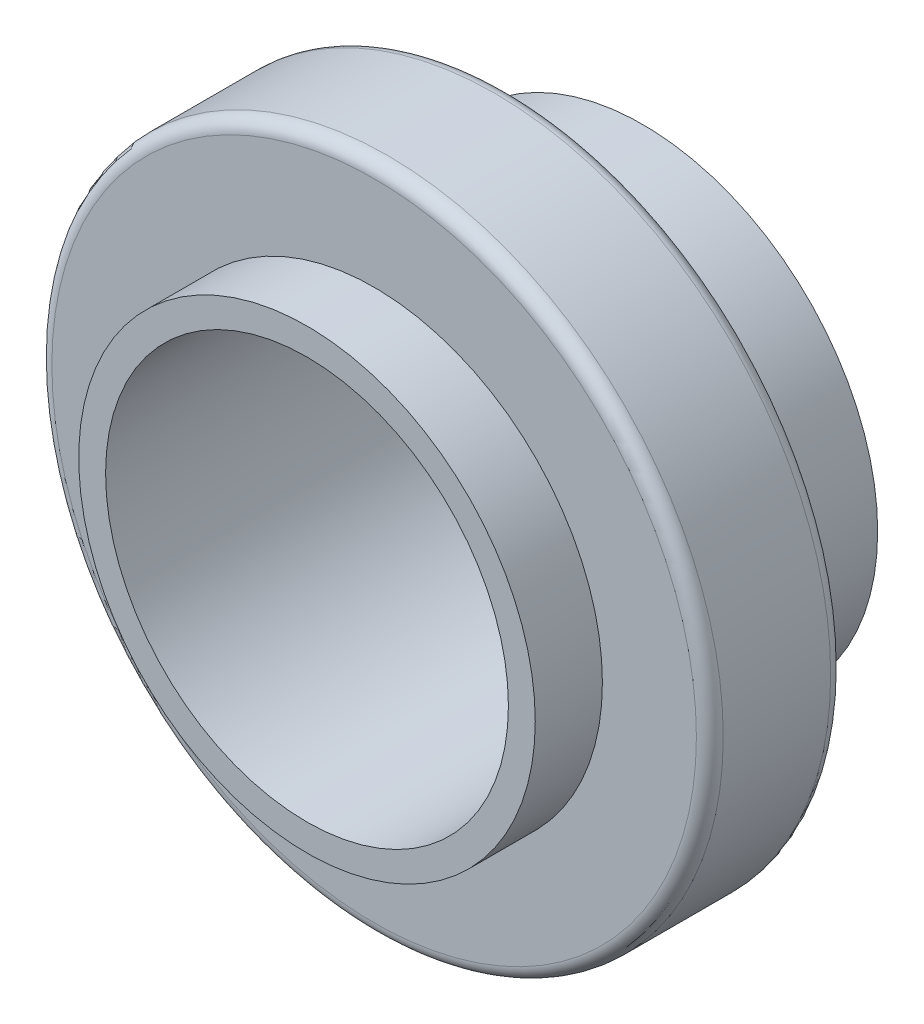
SolidWorks part; units mm, degrees
ref_plane "Front Plane" through (0, 0, 0) normal (0, 0, 1) x (1, 0, 0)
ref_plane "Top Plane" through (0, 0, 0) normal (0, 1, 0) x (1, 0, 0)
ref_plane "Right Plane" through (0, 0, 0) normal (1, 0, 0) x (0, 0, -1)
sketch "Sketch1" plane through (0, 0, 0) normal (0, 0, 1) x (1, 0, 0)
  circle A0 centre (0, 0) radius 17.5
  dimension "D1" = 35
extrude "Boss-Extrude1" add sketch "Sketch1" along normal blind 10
sketch "Sketch2" plane through (0, 0, 10) normal (0, 0, 1) x (1, 0, 0)
  circle A0 centre (0, 0) radius 25
  dimension "D1" = 50
extrude "Boss-Extrude2" add sketch "Sketch2" along normal blind 10
sketch "Sketch3" plane through (0, 0, 20) normal (0, 0, 1) x (1, 0, 0)
  circle A0 centre (0, 0) radius 17
  dimension "D1" = 34
extrude "Boss-Extrude3" add sketch "Sketch3" along normal blind 5
sketch "Sketch4" plane through (0, 0, 25) normal (0, 0, 1) x (1, 0, 0)
  circle A0 centre (0, 0) radius 15
  dimension "D1" = 30
extrude "Cut-Extrude1" cut sketch "Sketch4" against normal through all both and the other way through all
fillet "Fillet1" radius 1 2 edges at (25, 0, 20) (25, 0, 10)
